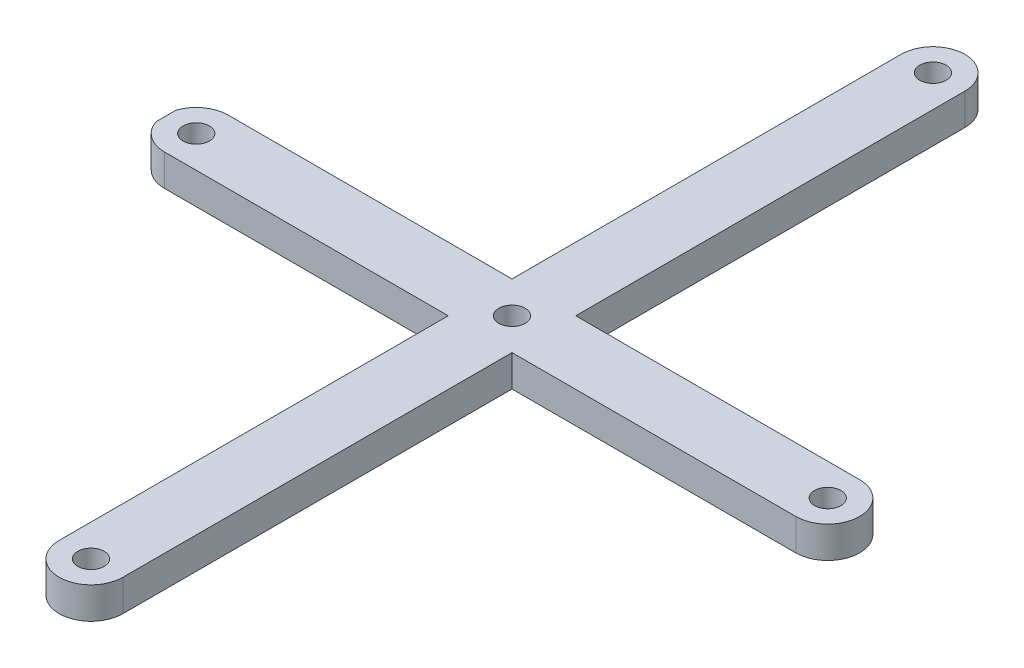
SolidWorks part; units mm, degrees
ref_plane "Front Plane" through (0, 0, 0) normal (0, 0, 1) x (1, 0, 0)
ref_plane "Top Plane" through (0, 0, 0) normal (0, 1, 0) x (1, 0, 0)
ref_plane "Right Plane" through (0, 0, 0) normal (1, 0, 0) x (0, 0, -1)
sketch "Sketch1" plane through (0, 0, 0) normal (0, 1, 0) x (1, 0, 0)
  line L0 (2.4545, 10.8182) -> (2.4545, 3.4242)
  line L6 (-4.1515, 2.8182) -> (-4.1515, 3.4242)
  line L8 (1.8485, 3.4242) -> (1.8485, 4.1212)
  line L16 (-4.7273, 3.0074) -> (-4.7273, 2.6289)
  line L21 (1.2424, 2.2121) -> (1.2424, -5.1818)
  line L22 (7.8485, 3.4242) -> (-4.1515, 3.4242)
  line L23 (1.2424, 2.2121) -> (-4.1515, 2.2121)
  line L25 (1.2424, 3.4242) -> (1.2424, 10.8182)
  line L26 (1.8485, -4.9318) -> (1.8485, -5.1818) construction
  line L27 (2.4545, 2.2121) -> (7.8485, 2.2121)
  line L28 (2.4545, 2.8182) -> (2.4545, -5.1818)
  line L29 (7.5985, 2.8182) -> (9.2293, 2.8182) construction
  circle A1 centre (-4.1515, 2.8182) radius 0.25
  circle A2 centre (1.8485, -5.1818) radius 0.25
  arc A3 (1.2424, -5.1818) -> (2.4545, -5.1818) centre (1.8485, -5.1818) ccw
  arc A4 (-4.1515, 3.4242) -> (-4.1515, 2.2121) centre (-4.1515, 2.8182) ccw
  arc A5 (1.2424, 10.8182) -> (2.4545, 10.8182) centre (1.8485, 10.8182) cw
  circle A6 centre (1.8485, 10.8182) radius 0.25
  circle A7 centre (7.8485, 2.8182) radius 0.25
  arc A8 (7.8485, 3.4242) -> (7.8485, 2.2121) centre (7.8485, 2.8182) cw
  dimension "D3" = 0.5
  dimension "D4" = 0.5
extrude "Boss-Extrude1" add sketch "Sketch1" along normal blind 0.6
sketch "Sketch2" plane through (0, 0.6, 0) normal (0, 1, 0) x (1, 0, 0)
  line L0 (-4.1515, 2.8182) -> (7.8485, 2.8182) construction
  line L1 (1.8485, 10.8182) -> (1.8485, -5.1818) construction
  circle A0 centre (1.8485, 2.8182) radius 0.25
  dimension "D1" = 0.5
extrude "Cut-Extrude1" cut sketch "Sketch2" against normal through all
